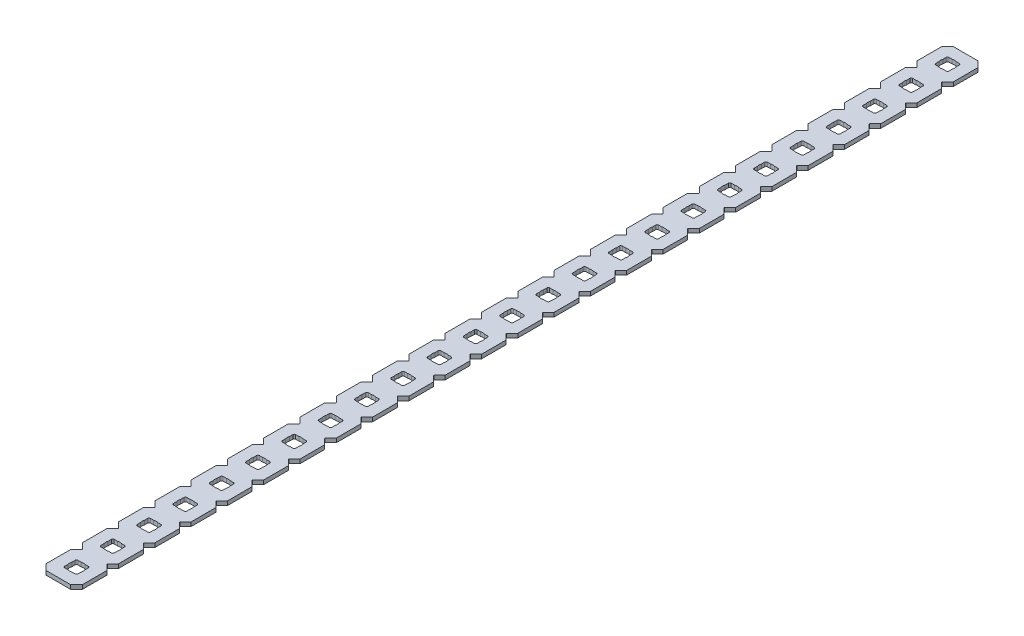
SolidWorks part; units mm, degrees
material "Custom Plastic"
ref_plane "Front Plane" through (0, 0, 0) normal (0, 0, 1) x (1, 0, 0)
ref_plane "Top Plane" through (0, 0, 0) normal (0, 1, 0) x (1, 0, 0)
ref_plane "Right Plane" through (0, 0, 0) normal (1, 0, 0) x (0, 0, -1)
ref_plane "Plane1" through (0, 0, 0) normal (0, -1, 0) x (1, 0, 0)
sketch "Sketch1" plane through (0, 0, 0) normal (0, -1, 0) x (1, 0, 0)
  line L0 (4.5466, -308.8386) -> (8.1534, -308.8386)
  line L1 (8.6614, -309.3466) -> (8.6614, -312.9534)
  line L2 (8.1534, -313.4614) -> (4.5466, -313.4614)
  line L3 (4.0386, -312.9534) -> (4.0386, -309.3466)
  line L4 (4.5466, -296.1386) -> (8.1534, -296.1386)
  line L5 (8.6614, -296.6466) -> (8.6614, -300.2534)
  line L6 (8.1534, -300.7614) -> (4.5466, -300.7614)
  line L7 (4.0386, -300.2534) -> (4.0386, -296.6466)
  line L8 (4.5466, -283.4386) -> (8.1534, -283.4386)
  line L9 (8.6614, -283.9466) -> (8.6614, -287.5534)
  line L10 (8.1534, -288.0614) -> (4.5466, -288.0614)
  line L11 (4.0386, -287.5534) -> (4.0386, -283.9466)
  line L12 (4.5466, -270.7386) -> (8.1534, -270.7386)
  line L13 (8.6614, -271.2466) -> (8.6614, -274.8534)
  line L14 (8.1534, -275.3614) -> (4.5466, -275.3614)
  line L15 (4.0386, -274.8534) -> (4.0386, -271.2466)
  line L16 (4.5466, -258.0386) -> (8.1534, -258.0386)
  line L17 (8.6614, -258.5466) -> (8.6614, -262.1534)
  line L18 (8.1534, -262.6614) -> (4.5466, -262.6614)
  line L19 (4.0386, -262.1534) -> (4.0386, -258.5466)
  line L20 (4.5466, -245.3386) -> (8.1534, -245.3386)
  line L21 (8.6614, -245.8466) -> (8.6614, -249.4534)
  line L22 (8.1534, -249.9614) -> (4.5466, -249.9614)
  line L23 (4.0386, -249.4534) -> (4.0386, -245.8466)
  line L24 (4.5466, -232.6386) -> (8.1534, -232.6386)
  line L25 (8.6614, -233.1466) -> (8.6614, -236.7534)
  line L26 (8.1534, -237.2614) -> (4.5466, -237.2614)
  line L27 (4.0386, -236.7534) -> (4.0386, -233.1466)
  line L28 (4.5466, -219.9386) -> (8.1534, -219.9386)
  line L29 (8.6614, -220.4466) -> (8.6614, -224.0534)
  line L30 (8.1534, -224.5614) -> (4.5466, -224.5614)
  line L31 (4.0386, -224.0534) -> (4.0386, -220.4466)
  line L32 (4.5466, -207.2386) -> (8.1534, -207.2386)
  line L33 (8.6614, -207.7466) -> (8.6614, -211.3534)
  line L34 (8.1534, -211.8614) -> (4.5466, -211.8614)
  line L35 (4.0386, -211.3534) -> (4.0386, -207.7466)
  line L36 (4.5466, -194.5386) -> (8.1534, -194.5386)
  line L37 (8.6614, -195.0466) -> (8.6614, -198.6534)
  line L38 (8.1534, -199.1614) -> (4.5466, -199.1614)
  line L39 (4.0386, -198.6534) -> (4.0386, -195.0466)
  line L40 (4.5466, -181.8386) -> (8.1534, -181.8386)
  line L41 (8.6614, -182.3466) -> (8.6614, -185.9534)
  line L42 (8.1534, -186.4614) -> (4.5466, -186.4614)
  line L43 (4.0386, -185.9534) -> (4.0386, -182.3466)
  line L44 (4.5466, -169.1386) -> (8.1534, -169.1386)
  line L45 (8.6614, -169.6466) -> (8.6614, -173.2534)
  line L46 (8.1534, -173.7614) -> (4.5466, -173.7614)
  line L47 (4.0386, -173.2534) -> (4.0386, -169.6466)
  line L48 (4.5466, -156.4386) -> (8.1534, -156.4386)
  line L49 (8.6614, -156.9466) -> (8.6614, -160.5534)
  line L50 (8.1534, -161.0614) -> (4.5466, -161.0614)
  line L51 (4.0386, -160.5534) -> (4.0386, -156.9466)
  line L52 (4.5466, -143.7386) -> (8.1534, -143.7386)
  line L53 (8.6614, -144.2466) -> (8.6614, -147.8534)
  line L54 (8.1534, -148.3614) -> (4.5466, -148.3614)
  line L55 (4.0386, -147.8534) -> (4.0386, -144.2466)
  line L56 (4.5466, -131.0386) -> (8.1534, -131.0386)
  line L57 (8.6614, -131.5466) -> (8.6614, -135.1534)
  line L58 (8.1534, -135.6614) -> (4.5466, -135.6614)
  line L59 (4.0386, -135.1534) -> (4.0386, -131.5466)
  line L60 (4.5466, -118.3386) -> (8.1534, -118.3386)
  line L61 (8.6614, -118.8466) -> (8.6614, -122.4534)
  line L62 (8.1534, -122.9614) -> (4.5466, -122.9614)
  line L63 (4.0386, -122.4534) -> (4.0386, -118.8466)
  line L64 (4.5466, -105.6386) -> (8.1534, -105.6386)
  line L65 (8.6614, -106.1466) -> (8.6614, -109.7534)
  line L66 (8.1534, -110.2614) -> (4.5466, -110.2614)
  line L67 (4.0386, -109.7534) -> (4.0386, -106.1466)
  line L68 (4.5466, -92.9386) -> (8.1534, -92.9386)
  line L69 (8.6614, -93.4466) -> (8.6614, -97.0534)
  line L70 (8.1534, -97.5614) -> (4.5466, -97.5614)
  line L71 (4.0386, -97.0534) -> (4.0386, -93.4466)
  line L72 (4.5466, -80.2386) -> (8.1534, -80.2386)
  line L73 (8.6614, -80.7466) -> (8.6614, -84.3534)
  line L74 (8.1534, -84.8614) -> (4.5466, -84.8614)
  line L75 (4.0386, -84.3534) -> (4.0386, -80.7466)
  line L76 (4.5466, -67.5386) -> (8.1534, -67.5386)
  line L77 (8.6614, -68.0466) -> (8.6614, -71.6534)
  line L78 (8.1534, -72.1614) -> (4.5466, -72.1614)
  line L79 (4.0386, -71.6534) -> (4.0386, -68.0466)
  line L80 (4.5466, -54.8386) -> (8.1534, -54.8386)
  line L81 (8.6614, -55.3466) -> (8.6614, -58.9534)
  line L82 (8.1534, -59.4614) -> (4.5466, -59.4614)
  line L83 (4.0386, -58.9534) -> (4.0386, -55.3466)
  line L84 (4.5466, -42.1386) -> (8.1534, -42.1386)
  line L85 (8.6614, -42.6466) -> (8.6614, -46.2534)
  line L86 (8.1534, -46.7614) -> (4.5466, -46.7614)
  line L87 (4.0386, -46.2534) -> (4.0386, -42.6466)
  line L88 (4.5466, -29.4386) -> (8.1534, -29.4386)
  line L89 (8.6614, -29.9466) -> (8.6614, -33.5534)
  line L90 (8.1534, -34.0614) -> (4.5466, -34.0614)
  line L91 (4.0386, -33.5534) -> (4.0386, -29.9466)
  line L92 (12.7, -302.773) -> (12.7, -294.127)
  line L93 (12.7, -294.127) -> (10.7628, -292.1898)
  line L94 (10.7628, -292.0102) -> (12.7, -290.073)
  line L95 (12.7, -290.073) -> (12.7, -281.427)
  line L96 (12.7, -281.427) -> (10.7628, -279.4898)
  line L97 (10.7628, -279.3102) -> (12.7, -277.373)
  line L98 (12.7, -277.373) -> (12.7, -268.727)
  line L99 (12.7, -268.727) -> (10.7628, -266.7898)
  line L100 (10.7628, -266.6102) -> (12.7, -264.673)
  line L101 (12.7, -264.673) -> (12.7, -256.027)
  line L102 (12.7, -256.027) -> (10.7628, -254.0898)
  line L103 (10.7628, -253.9102) -> (12.7, -251.973)
  line L104 (12.7, -251.973) -> (12.7, -243.327)
  line L105 (12.7, -243.327) -> (10.7628, -241.3898)
  line L106 (10.7628, -241.2102) -> (12.7, -239.273)
  line L107 (12.7, -239.273) -> (12.7, -230.627)
  line L108 (12.7, -230.627) -> (10.7628, -228.6898)
  line L109 (10.7628, -228.5102) -> (12.7, -226.573)
  line L110 (12.7, -226.573) -> (12.7, -217.927)
  line L111 (12.7, -217.927) -> (10.7628, -215.9898)
  line L112 (10.7628, -215.8102) -> (12.7, -213.873)
  line L113 (12.7, -213.873) -> (12.7, -205.227)
  line L114 (12.7, -205.227) -> (10.7628, -203.2898)
  line L115 (10.7628, -203.1102) -> (12.7, -201.173)
  line L116 (12.7, -201.173) -> (12.7, -192.527)
  line L117 (12.7, -192.527) -> (10.7628, -190.5898)
  line L118 (10.7628, -190.4102) -> (12.7, -188.473)
  line L119 (12.7, -188.473) -> (12.7, -179.827)
  line L120 (12.7, -179.827) -> (10.7628, -177.8898)
  line L121 (10.7628, -177.7102) -> (12.7, -175.773)
  line L122 (12.7, -175.773) -> (12.7, -167.127)
  line L123 (12.7, -167.127) -> (10.7628, -165.1898)
  line L124 (10.7628, -165.0102) -> (12.7, -163.073)
  line L125 (12.7, -163.073) -> (12.7, -154.427)
  line L126 (12.7, -154.427) -> (10.7628, -152.4898)
  line L127 (10.7628, -152.3102) -> (12.7, -150.373)
  line L128 (12.7, -150.373) -> (12.7, -141.727)
  line L129 (12.7, -141.727) -> (10.7628, -139.7898)
  line L130 (10.7628, -139.6102) -> (12.7, -137.673)
  line L131 (12.7, -137.673) -> (12.7, -129.027)
  line L132 (12.7, -129.027) -> (10.7628, -127.0898)
  line L133 (10.7628, -126.9102) -> (12.7, -124.973)
  line L134 (12.7, -124.973) -> (12.7, -116.327)
  line L135 (12.7, -116.327) -> (10.7628, -114.3898)
  line L136 (10.7628, -114.2102) -> (12.7, -112.273)
  line L137 (12.7, -112.273) -> (12.7, -103.627)
  line L138 (12.7, -103.627) -> (10.7628, -101.6898)
  line L139 (10.7628, -101.5102) -> (12.7, -99.573)
  line L140 (12.7, -99.573) -> (12.7, -90.927)
  line L141 (12.7, -90.927) -> (10.7628, -88.9898)
  line L142 (10.7628, -88.8102) -> (12.7, -86.873)
  line L143 (12.7, -86.873) -> (12.7, -78.227)
  line L144 (12.7, -78.227) -> (10.7628, -76.2898)
  line L145 (10.7628, -76.1102) -> (12.7, -74.173)
  line L146 (12.7, -74.173) -> (12.7, -65.527)
  line L147 (12.7, -65.527) -> (10.7628, -63.5898)
  line L148 (10.7628, -63.4102) -> (12.7, -61.473)
  line L149 (12.7, -61.473) -> (12.7, -52.827)
  line L150 (12.7, -52.827) -> (10.7628, -50.8898)
  line L151 (10.7628, -50.7102) -> (12.7, -48.773)
  line L152 (12.7, -48.773) -> (12.7, -40.127)
  line L153 (12.7, -40.127) -> (10.7628, -38.1898)
  line L154 (10.7628, -38.0102) -> (12.7, -36.073)
  line L155 (12.7, -36.073) -> (12.7, -27.427)
  line L156 (12.7, -27.427) -> (10.7628, -25.4898)
  line L157 (10.7628, -25.3102) -> (12.7, -23.373)
  line L158 (12.7, -23.373) -> (12.7, -14.727)
  line L159 (12.7, -14.727) -> (10.7628, -12.7898)
  line L160 (10.7628, -12.6102) -> (12.7, -10.673)
  line L161 (12.7, -10.673) -> (12.7, -2.032)
  line L162 (12.7, -2.032) -> (10.668, 0)
  line L163 (10.668, 0) -> (2.032, 0)
  line L164 (2.032, 0) -> (0, -2.032)
  line L165 (0, -2.032) -> (0, -10.673)
  line L166 (0, -10.673) -> (1.9372, -12.6102)
  line L167 (1.9372, -12.7898) -> (0, -14.727)
  line L168 (0, -14.727) -> (0, -23.373)
  line L169 (0, -23.373) -> (1.9372, -25.3102)
  line L170 (1.9372, -25.4898) -> (0, -27.427)
  line L171 (0, -27.427) -> (0, -36.073)
  line L172 (0, -36.073) -> (1.9372, -38.0102)
  line L173 (1.9372, -38.1898) -> (0, -40.127)
  line L174 (0, -40.127) -> (0, -48.773)
  line L175 (0, -48.773) -> (1.9372, -50.7102)
  line L176 (1.9372, -50.8898) -> (0, -52.827)
  line L177 (0, -52.827) -> (0, -61.473)
  line L178 (0, -61.473) -> (1.9372, -63.4102)
  line L179 (1.9372, -63.5898) -> (0, -65.527)
  line L180 (0, -65.527) -> (0, -74.173)
  line L181 (0, -74.173) -> (1.9372, -76.1102)
  line L182 (1.9372, -76.2898) -> (0, -78.227)
  line L183 (0, -78.227) -> (0, -86.873)
  line L184 (0, -86.873) -> (1.9372, -88.8102)
  line L185 (1.9372, -88.9898) -> (0, -90.927)
  line L186 (0, -90.927) -> (0, -99.573)
  line L187 (0, -99.573) -> (1.9372, -101.5102)
  line L188 (1.9372, -101.6898) -> (0, -103.627)
  line L189 (0, -103.627) -> (0, -112.273)
  line L190 (0, -112.273) -> (1.9372, -114.2102)
  line L191 (1.9372, -114.3898) -> (0, -116.327)
  line L192 (0, -116.327) -> (0, -124.973)
  line L193 (0, -124.973) -> (1.9372, -126.9102)
  line L194 (1.9372, -127.0898) -> (0, -129.027)
  line L195 (0, -129.027) -> (0, -137.673)
  line L196 (0, -137.673) -> (1.9372, -139.6102)
  line L197 (1.9372, -139.7898) -> (0, -141.727)
  line L198 (0, -141.727) -> (0, -150.373)
  line L199 (0, -150.373) -> (1.9372, -152.3102)
  line L200 (1.9372, -152.4898) -> (0, -154.427)
  line L201 (0, -154.427) -> (0, -163.073)
  line L202 (0, -163.073) -> (1.9372, -165.0102)
  line L203 (1.9372, -165.1898) -> (0, -167.127)
  line L204 (0, -167.127) -> (0, -175.773)
  line L205 (0, -175.773) -> (1.9372, -177.7102)
  line L206 (1.9372, -177.8898) -> (0, -179.827)
  line L207 (0, -179.827) -> (0, -188.473)
  line L208 (0, -188.473) -> (1.9372, -190.4102)
  line L209 (1.9372, -190.5898) -> (0, -192.527)
  line L210 (0, -192.527) -> (0, -201.173)
  line L211 (0, -201.173) -> (1.9372, -203.1102)
  line L212 (1.9372, -203.2898) -> (0, -205.227)
  line L213 (0, -205.227) -> (0, -213.873)
  line L214 (0, -213.873) -> (1.9372, -215.8102)
  line L215 (1.9372, -215.9898) -> (0, -217.927)
  line L216 (0, -217.927) -> (0, -226.573)
  line L217 (0, -226.573) -> (1.9372, -228.5102)
  line L218 (1.9372, -228.6898) -> (0, -230.627)
  line L219 (0, -230.627) -> (0, -239.273)
  line L220 (0, -239.273) -> (1.9372, -241.2102)
  line L221 (1.9372, -241.3898) -> (0, -243.327)
  line L222 (0, -243.327) -> (0, -251.973)
  line L223 (0, -251.973) -> (1.9372, -253.9102)
  line L224 (1.9372, -254.0898) -> (0, -256.027)
  line L225 (0, -256.027) -> (0, -264.673)
  line L226 (0, -264.673) -> (1.9372, -266.6102)
  line L227 (1.9372, -266.7898) -> (0, -268.727)
  line L228 (0, -268.727) -> (0, -277.373)
  line L229 (0, -277.373) -> (1.9372, -279.3102)
  line L230 (1.9372, -279.4898) -> (0, -281.427)
  line L231 (0, -281.427) -> (0, -290.073)
  line L232 (0, -290.073) -> (1.9372, -292.0102)
  line L233 (1.9372, -292.1898) -> (0, -294.127)
  line L234 (0, -294.127) -> (0, -302.773)
  line L235 (0, -302.773) -> (1.9372, -304.7102)
  line L236 (1.9372, -304.8898) -> (0, -306.827)
  line L237 (0, -306.827) -> (0, -315.468)
  line L238 (0, -315.468) -> (2.032, -317.5)
  line L239 (2.032, -317.5) -> (10.668, -317.5)
  line L240 (10.668, -317.5) -> (12.7, -315.468)
  line L241 (12.7, -315.468) -> (12.7, -306.827)
  line L242 (12.7, -306.827) -> (10.7628, -304.8898)
  line L243 (10.7628, -304.7102) -> (12.7, -302.773)
  line L244 (8.1534, -8.6614) -> (4.5466, -8.6614)
  line L245 (4.0386, -8.1534) -> (4.0386, -4.5466)
  line L246 (4.5466, -4.0386) -> (8.1534, -4.0386)
  line L247 (8.6614, -4.5466) -> (8.6614, -8.1534)
  line L248 (4.0386, -20.8534) -> (4.0386, -17.2466)
  line L249 (4.5466, -16.7386) -> (8.1534, -16.7386)
  line L250 (8.6614, -17.2466) -> (8.6614, -20.8534)
  line L251 (8.1534, -21.3614) -> (4.5466, -21.3614)
  arc A0 (4.0386, -309.3466) -> (4.5466, -308.8386) centre (4.5466, -309.3466) cw
  arc A1 (8.1534, -308.8386) -> (8.6614, -309.3466) centre (8.1534, -309.3466) cw
  arc A2 (8.6614, -312.9534) -> (8.1534, -313.4614) centre (8.1534, -312.9534) cw
  arc A3 (4.5466, -313.4614) -> (4.0386, -312.9534) centre (4.5466, -312.9534) cw
  arc A4 (4.0386, -296.6466) -> (4.5466, -296.1386) centre (4.5466, -296.6466) cw
  arc A5 (8.1534, -296.1386) -> (8.6614, -296.6466) centre (8.1534, -296.6466) cw
  arc A6 (8.6614, -300.2534) -> (8.1534, -300.7614) centre (8.1534, -300.2534) cw
  arc A7 (4.5466, -300.7614) -> (4.0386, -300.2534) centre (4.5466, -300.2534) cw
  arc A8 (4.0386, -283.9466) -> (4.5466, -283.4386) centre (4.5466, -283.9466) cw
  arc A9 (8.1534, -283.4386) -> (8.6614, -283.9466) centre (8.1534, -283.9466) cw
  arc A10 (8.6614, -287.5534) -> (8.1534, -288.0614) centre (8.1534, -287.5534) cw
  arc A11 (4.5466, -288.0614) -> (4.0386, -287.5534) centre (4.5466, -287.5534) cw
  arc A12 (4.0386, -271.2466) -> (4.5466, -270.7386) centre (4.5466, -271.2466) cw
  arc A13 (8.1534, -270.7386) -> (8.6614, -271.2466) centre (8.1534, -271.2466) cw
  arc A14 (8.6614, -274.8534) -> (8.1534, -275.3614) centre (8.1534, -274.8534) cw
  arc A15 (4.5466, -275.3614) -> (4.0386, -274.8534) centre (4.5466, -274.8534) cw
  arc A16 (4.0386, -258.5466) -> (4.5466, -258.0386) centre (4.5466, -258.5466) cw
  arc A17 (8.1534, -258.0386) -> (8.6614, -258.5466) centre (8.1534, -258.5466) cw
  arc A18 (8.6614, -262.1534) -> (8.1534, -262.6614) centre (8.1534, -262.1534) cw
  arc A19 (4.5466, -262.6614) -> (4.0386, -262.1534) centre (4.5466, -262.1534) cw
  arc A20 (4.0386, -245.8466) -> (4.5466, -245.3386) centre (4.5466, -245.8466) cw
  arc A21 (8.1534, -245.3386) -> (8.6614, -245.8466) centre (8.1534, -245.8466) cw
  arc A22 (8.6614, -249.4534) -> (8.1534, -249.9614) centre (8.1534, -249.4534) cw
  arc A23 (4.5466, -249.9614) -> (4.0386, -249.4534) centre (4.5466, -249.4534) cw
  arc A24 (4.0386, -233.1466) -> (4.5466, -232.6386) centre (4.5466, -233.1466) cw
  arc A25 (8.1534, -232.6386) -> (8.6614, -233.1466) centre (8.1534, -233.1466) cw
  arc A26 (8.6614, -236.7534) -> (8.1534, -237.2614) centre (8.1534, -236.7534) cw
  arc A27 (4.5466, -237.2614) -> (4.0386, -236.7534) centre (4.5466, -236.7534) cw
  arc A28 (4.0386, -220.4466) -> (4.5466, -219.9386) centre (4.5466, -220.4466) cw
  arc A29 (8.1534, -219.9386) -> (8.6614, -220.4466) centre (8.1534, -220.4466) cw
  arc A30 (8.6614, -224.0534) -> (8.1534, -224.5614) centre (8.1534, -224.0534) cw
  arc A31 (4.5466, -224.5614) -> (4.0386, -224.0534) centre (4.5466, -224.0534) cw
  arc A32 (4.0386, -207.7466) -> (4.5466, -207.2386) centre (4.5466, -207.7466) cw
  arc A33 (8.1534, -207.2386) -> (8.6614, -207.7466) centre (8.1534, -207.7466) cw
  arc A34 (8.6614, -211.3534) -> (8.1534, -211.8614) centre (8.1534, -211.3534) cw
  arc A35 (4.5466, -211.8614) -> (4.0386, -211.3534) centre (4.5466, -211.3534) cw
  arc A36 (4.0386, -195.0466) -> (4.5466, -194.5386) centre (4.5466, -195.0466) cw
  arc A37 (8.1534, -194.5386) -> (8.6614, -195.0466) centre (8.1534, -195.0466) cw
  arc A38 (8.6614, -198.6534) -> (8.1534, -199.1614) centre (8.1534, -198.6534) cw
  arc A39 (4.5466, -199.1614) -> (4.0386, -198.6534) centre (4.5466, -198.6534) cw
  arc A40 (4.0386, -182.3466) -> (4.5466, -181.8386) centre (4.5466, -182.3466) cw
  arc A41 (8.1534, -181.8386) -> (8.6614, -182.3466) centre (8.1534, -182.3466) cw
  arc A42 (8.6614, -185.9534) -> (8.1534, -186.4614) centre (8.1534, -185.9534) cw
  arc A43 (4.5466, -186.4614) -> (4.0386, -185.9534) centre (4.5466, -185.9534) cw
  arc A44 (4.0386, -169.6466) -> (4.5466, -169.1386) centre (4.5466, -169.6466) cw
  arc A45 (8.1534, -169.1386) -> (8.6614, -169.6466) centre (8.1534, -169.6466) cw
  arc A46 (8.6614, -173.2534) -> (8.1534, -173.7614) centre (8.1534, -173.2534) cw
  arc A47 (4.5466, -173.7614) -> (4.0386, -173.2534) centre (4.5466, -173.2534) cw
  arc A48 (4.0386, -156.9466) -> (4.5466, -156.4386) centre (4.5466, -156.9466) cw
  arc A49 (8.1534, -156.4386) -> (8.6614, -156.9466) centre (8.1534, -156.9466) cw
  arc A50 (8.6614, -160.5534) -> (8.1534, -161.0614) centre (8.1534, -160.5534) cw
  arc A51 (4.5466, -161.0614) -> (4.0386, -160.5534) centre (4.5466, -160.5534) cw
  arc A52 (4.0386, -144.2466) -> (4.5466, -143.7386) centre (4.5466, -144.2466) cw
  arc A53 (8.1534, -143.7386) -> (8.6614, -144.2466) centre (8.1534, -144.2466) cw
  arc A54 (8.6614, -147.8534) -> (8.1534, -148.3614) centre (8.1534, -147.8534) cw
  arc A55 (4.5466, -148.3614) -> (4.0386, -147.8534) centre (4.5466, -147.8534) cw
  arc A56 (4.0386, -131.5466) -> (4.5466, -131.0386) centre (4.5466, -131.5466) cw
  arc A57 (8.1534, -131.0386) -> (8.6614, -131.5466) centre (8.1534, -131.5466) cw
  arc A58 (8.6614, -135.1534) -> (8.1534, -135.6614) centre (8.1534, -135.1534) cw
  arc A59 (4.5466, -135.6614) -> (4.0386, -135.1534) centre (4.5466, -135.1534) cw
  arc A60 (4.0386, -118.8466) -> (4.5466, -118.3386) centre (4.5466, -118.8466) cw
  arc A61 (8.1534, -118.3386) -> (8.6614, -118.8466) centre (8.1534, -118.8466) cw
  arc A62 (8.6614, -122.4534) -> (8.1534, -122.9614) centre (8.1534, -122.4534) cw
  arc A63 (4.5466, -122.9614) -> (4.0386, -122.4534) centre (4.5466, -122.4534) cw
  arc A64 (4.0386, -106.1466) -> (4.5466, -105.6386) centre (4.5466, -106.1466) cw
  arc A65 (8.1534, -105.6386) -> (8.6614, -106.1466) centre (8.1534, -106.1466) cw
  arc A66 (8.6614, -109.7534) -> (8.1534, -110.2614) centre (8.1534, -109.7534) cw
  arc A67 (4.5466, -110.2614) -> (4.0386, -109.7534) centre (4.5466, -109.7534) cw
  arc A68 (4.0386, -93.4466) -> (4.5466, -92.9386) centre (4.5466, -93.4466) cw
  arc A69 (8.1534, -92.9386) -> (8.6614, -93.4466) centre (8.1534, -93.4466) cw
  arc A70 (8.6614, -97.0534) -> (8.1534, -97.5614) centre (8.1534, -97.0534) cw
  arc A71 (4.5466, -97.5614) -> (4.0386, -97.0534) centre (4.5466, -97.0534) cw
  arc A72 (4.0386, -80.7466) -> (4.5466, -80.2386) centre (4.5466, -80.7466) cw
  arc A73 (8.1534, -80.2386) -> (8.6614, -80.7466) centre (8.1534, -80.7466) cw
  arc A74 (8.6614, -84.3534) -> (8.1534, -84.8614) centre (8.1534, -84.3534) cw
  arc A75 (4.5466, -84.8614) -> (4.0386, -84.3534) centre (4.5466, -84.3534) cw
  arc A76 (4.0386, -68.0466) -> (4.5466, -67.5386) centre (4.5466, -68.0466) cw
  arc A77 (8.1534, -67.5386) -> (8.6614, -68.0466) centre (8.1534, -68.0466) cw
  arc A78 (8.6614, -71.6534) -> (8.1534, -72.1614) centre (8.1534, -71.6534) cw
  arc A79 (4.5466, -72.1614) -> (4.0386, -71.6534) centre (4.5466, -71.6534) cw
  arc A80 (4.0386, -55.3466) -> (4.5466, -54.8386) centre (4.5466, -55.3466) cw
  arc A81 (8.1534, -54.8386) -> (8.6614, -55.3466) centre (8.1534, -55.3466) cw
  arc A82 (8.6614, -58.9534) -> (8.1534, -59.4614) centre (8.1534, -58.9534) cw
  arc A83 (4.5466, -59.4614) -> (4.0386, -58.9534) centre (4.5466, -58.9534) cw
  arc A84 (4.0386, -42.6466) -> (4.5466, -42.1386) centre (4.5466, -42.6466) cw
  arc A85 (8.1534, -42.1386) -> (8.6614, -42.6466) centre (8.1534, -42.6466) cw
  arc A86 (8.6614, -46.2534) -> (8.1534, -46.7614) centre (8.1534, -46.2534) cw
  arc A87 (4.5466, -46.7614) -> (4.0386, -46.2534) centre (4.5466, -46.2534) cw
  arc A88 (4.0386, -29.9466) -> (4.5466, -29.4386) centre (4.5466, -29.9466) cw
  arc A89 (8.1534, -29.4386) -> (8.6614, -29.9466) centre (8.1534, -29.9466) cw
  arc A90 (8.6614, -33.5534) -> (8.1534, -34.0614) centre (8.1534, -33.5534) cw
  arc A91 (4.5466, -34.0614) -> (4.0386, -33.5534) centre (4.5466, -33.5534) cw
  arc A92 (10.7628, -292.1898) -> (10.7628, -292.0102) centre (10.8526, -292.1) cw
  arc A93 (10.7628, -279.4898) -> (10.7628, -279.3102) centre (10.8526, -279.4) cw
  arc A94 (10.7628, -266.7898) -> (10.7628, -266.6102) centre (10.8526, -266.7) cw
  arc A95 (10.7628, -254.0898) -> (10.7628, -253.9102) centre (10.8526, -254) cw
  arc A96 (10.7628, -241.3898) -> (10.7628, -241.2102) centre (10.8526, -241.3) cw
  arc A97 (10.7628, -228.6898) -> (10.7628, -228.5102) centre (10.8526, -228.6) cw
  arc A98 (10.7628, -215.9898) -> (10.7628, -215.8102) centre (10.8526, -215.9) cw
  arc A99 (10.7628, -203.2898) -> (10.7628, -203.1102) centre (10.8526, -203.2) cw
  arc A100 (10.7628, -190.5898) -> (10.7628, -190.4102) centre (10.8526, -190.5) cw
  arc A101 (10.7628, -177.8898) -> (10.7628, -177.7102) centre (10.8526, -177.8) cw
  arc A102 (10.7628, -165.1898) -> (10.7628, -165.0102) centre (10.8526, -165.1) cw
  arc A103 (10.7628, -152.4898) -> (10.7628, -152.3102) centre (10.8526, -152.4) cw
  arc A104 (10.7628, -139.7898) -> (10.7628, -139.6102) centre (10.8526, -139.7) cw
  arc A105 (10.7628, -127.0898) -> (10.7628, -126.9102) centre (10.8526, -127) cw
  arc A106 (10.7628, -114.3898) -> (10.7628, -114.2102) centre (10.8526, -114.3) cw
  arc A107 (10.7628, -101.6898) -> (10.7628, -101.5102) centre (10.8526, -101.6) cw
  arc A108 (10.7628, -88.9898) -> (10.7628, -88.8102) centre (10.8526, -88.9) cw
  arc A109 (10.7628, -76.2898) -> (10.7628, -76.1102) centre (10.8526, -76.2) cw
  arc A110 (10.7628, -63.5898) -> (10.7628, -63.4102) centre (10.8526, -63.5) cw
  arc A111 (10.7628, -50.8898) -> (10.7628, -50.7102) centre (10.8526, -50.8) cw
  arc A112 (10.7628, -38.1898) -> (10.7628, -38.0102) centre (10.8526, -38.1) cw
  arc A113 (10.7628, -25.4898) -> (10.7628, -25.3102) centre (10.8526, -25.4) cw
  arc A114 (10.7628, -12.7898) -> (10.7628, -12.6102) centre (10.8526, -12.7) cw
  arc A115 (1.9372, -12.6102) -> (1.9372, -12.7898) centre (1.8474, -12.7) cw
  arc A116 (1.9372, -25.3102) -> (1.9372, -25.4898) centre (1.8474, -25.4) cw
  arc A117 (1.9372, -38.0102) -> (1.9372, -38.1898) centre (1.8474, -38.1) cw
  arc A118 (1.9372, -50.7102) -> (1.9372, -50.8898) centre (1.8474, -50.8) cw
  arc A119 (1.9372, -63.4102) -> (1.9372, -63.5898) centre (1.8474, -63.5) cw
  arc A120 (1.9372, -76.1102) -> (1.9372, -76.2898) centre (1.8474, -76.2) cw
  arc A121 (1.9372, -88.8102) -> (1.9372, -88.9898) centre (1.8474, -88.9) cw
  arc A122 (1.9372, -101.5102) -> (1.9372, -101.6898) centre (1.8474, -101.6) cw
  arc A123 (1.9372, -114.2102) -> (1.9372, -114.3898) centre (1.8474, -114.3) cw
  arc A124 (1.9372, -126.9102) -> (1.9372, -127.0898) centre (1.8474, -127) cw
  arc A125 (1.9372, -139.6102) -> (1.9372, -139.7898) centre (1.8474, -139.7) cw
  arc A126 (1.9372, -152.3102) -> (1.9372, -152.4898) centre (1.8474, -152.4) cw
  arc A127 (1.9372, -165.0102) -> (1.9372, -165.1898) centre (1.8474, -165.1) cw
  arc A128 (1.9372, -177.7102) -> (1.9372, -177.8898) centre (1.8474, -177.8) cw
  arc A129 (1.9372, -190.4102) -> (1.9372, -190.5898) centre (1.8474, -190.5) cw
  arc A130 (1.9372, -203.1102) -> (1.9372, -203.2898) centre (1.8474, -203.2) cw
  arc A131 (1.9372, -215.8102) -> (1.9372, -215.9898) centre (1.8474, -215.9) cw
  arc A132 (1.9372, -228.5102) -> (1.9372, -228.6898) centre (1.8474, -228.6) cw
  arc A133 (1.9372, -241.2102) -> (1.9372, -241.3898) centre (1.8474, -241.3) cw
  arc A134 (1.9372, -253.9102) -> (1.9372, -254.0898) centre (1.8474, -254) cw
  arc A135 (1.9372, -266.6102) -> (1.9372, -266.7898) centre (1.8474, -266.7) cw
  arc A136 (1.9372, -279.3102) -> (1.9372, -279.4898) centre (1.8474, -279.4) cw
  arc A137 (1.9372, -292.0102) -> (1.9372, -292.1898) centre (1.8474, -292.1) cw
  arc A138 (1.9372, -304.7102) -> (1.9372, -304.8898) centre (1.8474, -304.8) cw
  arc A139 (10.7628, -304.8898) -> (10.7628, -304.7102) centre (10.8526, -304.8) cw
  arc A140 (8.6614, -8.1534) -> (8.1534, -8.6614) centre (8.1534, -8.1534) cw
  arc A141 (4.5466, -8.6614) -> (4.0386, -8.1534) centre (4.5466, -8.1534) cw
  arc A142 (4.0386, -4.5466) -> (4.5466, -4.0386) centre (4.5466, -4.5466) cw
  arc A143 (8.1534, -4.0386) -> (8.6614, -4.5466) centre (8.1534, -4.5466) cw
  arc A144 (4.0386, -17.2466) -> (4.5466, -16.7386) centre (4.5466, -17.2466) cw
  arc A145 (8.1534, -16.7386) -> (8.6614, -17.2466) centre (8.1534, -17.2466) cw
  arc A146 (8.6614, -20.8534) -> (8.1534, -21.3614) centre (8.1534, -20.8534) cw
  arc A147 (4.5466, -21.3614) -> (4.0386, -20.8534) centre (4.5466, -20.8534) cw
extrude "Boss-Extrude1" add sketch "Sketch1" against normal blind 1.4224
sketch "Sketch2" plane through (0, 1.4224, 0) normal (0, 1, 0) x (1, 0, 0)
  line L0 (6.35, 4.0386) -> (6.35, 8.6614) construction
  line L1 (8.1534, 4.0386) -> (4.5466, 4.0386) construction
  line L2 (4.5466, 8.6614) -> (8.1534, 8.6614) construction
  circle A0 centre (6.35, 6.35) radius 2.413
  dimension "D1" = 4.826
extrude "Cut-Extrude1" cut sketch "Sketch2" against normal blind 2.54
pattern_linear "LPattern1" count 25 spacing 12.7 along (0, 0, -1) of "Cut-Extrude1"
